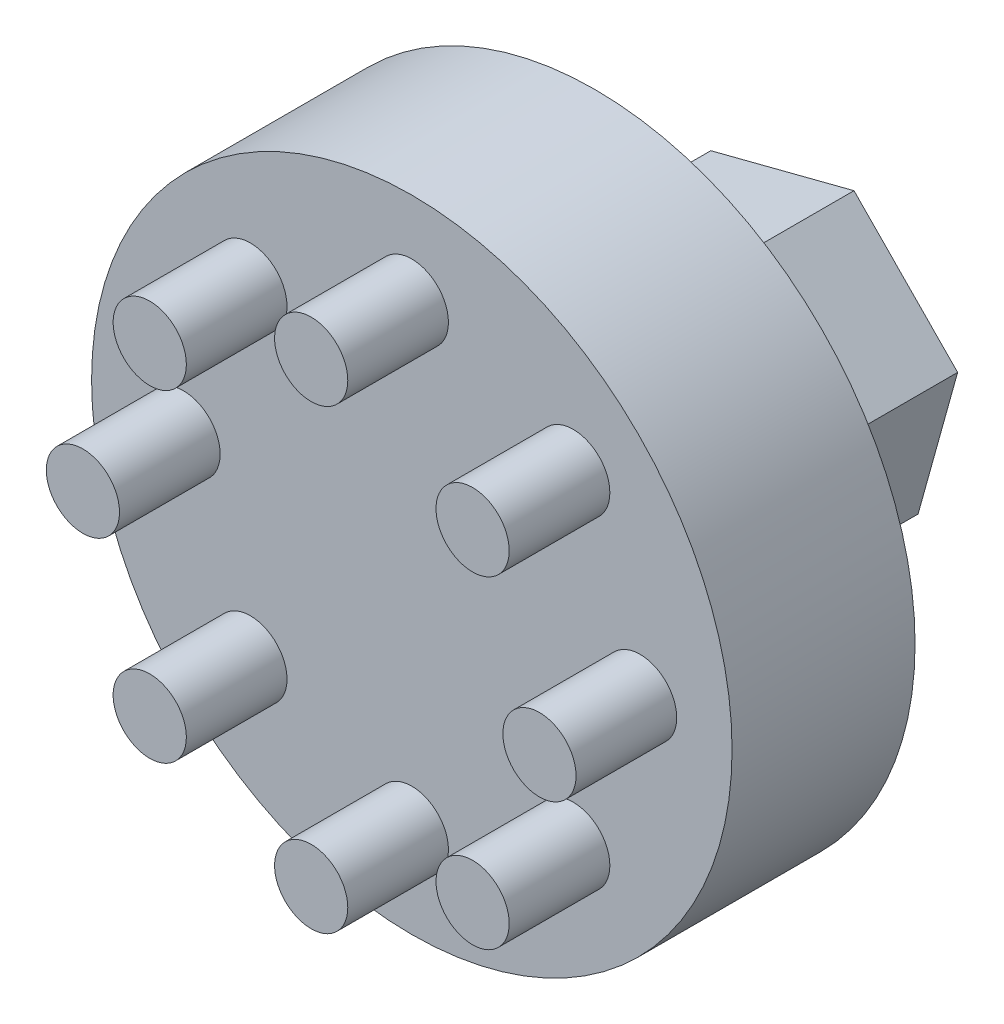
SolidWorks part; units mm, degrees
ref_plane "Plan de face" through (0, 0, 0) normal (0, 0, 1) x (1, 0, 0)
ref_plane "Plan de dessus" through (0, 0, 0) normal (0, 1, 0) x (1, 0, 0)
ref_plane "Plan de droite" through (0, 0, 0) normal (1, 0, 0) x (0, 0, -1)
sketch "Esquisse1" plane through (0, 0, 0) normal (0, 0, 1) x (1, 0, 0)
  circle A0 centre (0, 0) radius 17.5
  dimension "D1" = 35
extrude "Boss.-Extru.1" add sketch "Esquisse1" along normal blind 10
sketch "Esquisse2" plane through (0, 0, 10) normal (0, 0, 1) x (1, 0, 0)
  line L0 (0, -7.4151) -> (0, 22.91) construction
  line L1 (-5.5378, 0) -> (12.8145, 0) construction
  circle A0 centre (8.8212, 8.8212) radius 2
  circle A1 centre (0, 12.475) radius 2
  circle A2 centre (12.475, 0) radius 2
  circle A3 centre (8.8212, -8.8212) radius 2
  circle A4 centre (0, -12.475) radius 2
  circle A5 centre (-8.8212, -8.8212) radius 2
  circle A6 centre (-12.475, 0) radius 2
  circle A7 centre (-8.8212, 8.8212) radius 2
  point P24 (0, 0)
  dimension "D1" = 12.475
  dimension "D2" = 4
  dimension "D3" = 8
extrude "Boss.-Extru.2" add sketch "Esquisse2" along normal blind 5.5
sketch "Esquisse3" plane through (0, 0, 0) normal (0, 0, -1) x (-1, 0, 0)
  line L1 (5.6628, 5.7677) -> (-2.1636, 7.788)
  line L2 (-2.1636, 7.788) -> (-7.8264, 2.0203)
  line L3 (-7.8264, 2.0203) -> (-5.6628, -5.7677)
  line L4 (-5.6628, -5.7677) -> (2.1636, -7.788)
  line L5 (2.1636, -7.788) -> (7.8264, -2.0203)
  line L6 (7.8264, -2.0203) -> (5.6628, 5.7677)
  circle A0 centre (0, 0) radius 7 construction
  point P1 (1.7496, 6.7778)
  dimension "D1" = 14
extrude "Boss.-Extru.3" add sketch "Esquisse3" along normal blind 12
